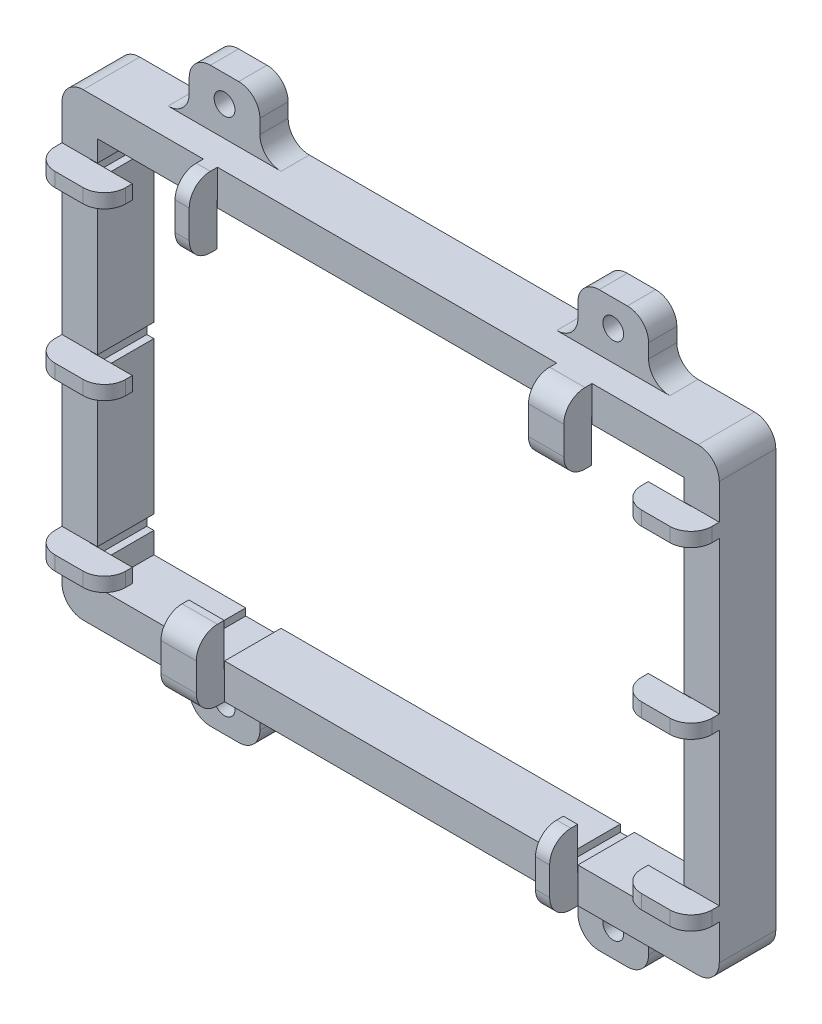
SolidWorks part; units mm, degrees
ref_plane "Front Plane" through (0, 0, 0) normal (0, 0, 1) x (1, 0, 0)
ref_plane "Top Plane" through (0, 0, 0) normal (0, 1, 0) x (1, 0, 0)
ref_plane "Right Plane" through (0, 0, 0) normal (1, 0, 0) x (0, 0, -1)
sketch "Sketch1" plane through (0, 0, 0) normal (0, 0, 1) x (1, 0, 0)
  line L0 (-41.5, 29.0054) -> (-46.5, 32.5) construction
  line L1 (41.5, -27.5) -> (-41.5, -27.5)
  line L2 (41.5, -27.5) -> (41.5, 27.5)
  line L3 (41.5, 27.5) -> (-41.5, 27.5)
  line L4 (-41.5, -27.5) -> (-41.5, 27.5)
  line L5 (0, -62.4654) -> (0, 68.7423) construction
  line L6 (-81.6773, -1.5) -> (70.6517, -1.5) construction
  line L7 (46.5, -32.5) -> (-46.5, -32.5)
  line L8 (46.5, -32.5) -> (46.5, 32.5)
  line L9 (46.5, 32.5) -> (-46.5, 32.5)
  line L10 (-46.5, -32.5) -> (-46.5, 32.5)
  line L11 (46.5, -32.5) -> (41.5, -29.0054) construction
  line L12 (46.5, 32.5) -> (41.5, 29.0054) construction
  line L13 (-41.5, -29.0054) -> (-46.5, -32.5) construction
  point P0 (0, 0)
  point P6 (0, 0)
  dimension "D1" = 83
  dimension "D2" = 55
  dimension "D3" = 5
  dimension "D4" = 5
  dimension "D5" = 5
  dimension "D6" = 5
extrude "Boss-Extrude1" add sketch "Sketch1" along normal blind 8
fillet "Fillet1" radius 3 4 edges at (-46.5, -32.5, 4) (-46.5, 32.5, 4) (46.5, -32.5, 4) (46.5, 32.5, 4)
sketch "Sketch2" plane through (0, 32.5, 0) normal (0, 1, 0) x (1, 0, 0)
  line L0 (-43.5, 0) -> (-43.5, -8) construction
  line L1 (-32.5, 0) -> (-22.5, 0)
  line L2 (-32.5, 0) -> (-32.5, -4)
  line L3 (-32.5, -4) -> (-22.5, -4)
  line L4 (-22.5, 0) -> (-22.5, -4)
  line L5 (-32.5, 0) -> (-22.5, -4) construction
  line L6 (-32.5, -4) -> (-22.5, 0) construction
  line L7 (22.5, 0) -> (32.5, 0)
  line L8 (22.5, 0) -> (22.5, -4)
  line L9 (22.5, -4) -> (32.5, -4)
  line L10 (32.5, 0) -> (32.5, -4)
  line L11 (22.5, 0) -> (32.5, -4) construction
  line L12 (22.5, -4) -> (32.5, 0) construction
  line L13 (43.5, -8) -> (43.5, 0) construction
  line L16 (43.5, 0) -> (-43.5, 0) construction
  line L17 (43.5, -8) -> (-43.5, -8) construction
  point P0 (-27.5, -2)
  point P5 (27.5, -2)
  dimension "D1" = 10
  dimension "D2" = 10
  dimension "D3" = 11
  dimension "D4" = 11
  dimension "D5" = 0
  dimension "D6" = 0
  dimension "D7" = 4
  dimension "D8" = 4
extrude "Boss-Extrude6" add sketch "Sketch2" along normal blind 8
mirror "Mirror2" about plane through (0, 0, 0) normal (0, 1, 0) of "Boss-Extrude6"
fillet "Fillet3" radius 3 8 edges at (32.5, -32.5, 2) (22.5, -32.5, 2) (-22.5, -32.5, 2) (-32.5, -32.5, 2) (-32.5, 32.5, 2) (-22.5, 32.5, 2) (22.5, 32.5, 2) (32.5, 32.5, 2)
sketch "Sketch9" plane through (0, 0, 4) normal (0, 0, 1) x (1, 0, 0)
  circle A1 centre (27.5, -36.7427) radius 1.47
  dimension "D1" = 2.94
extrude "Cut-Extrude1" cut sketch "Sketch9" against normal through all
mirror "Mirror3" about plane through (0, 0, 0) normal (1, 0, 0) of "Cut-Extrude1"
mirror "Mirror4" about plane through (0, 0, 0) normal (0, 1, 0) of "Mirror3", "Cut-Extrude1"
sketch "Sketch10" plane through (0, 0, 0) normal (0, 0, -1) x (-1, 0, 0)
  line L0 (41.5, -27.5) -> (-41.5, -27.5) construction
  line L1 (-24.5, -27.5) -> (-26.5, -27.5)
  line L2 (-24.5, -27.5) -> (-24.5, -28.5)
  line L3 (-24.5, -28.5) -> (-26.5, -28.5)
  line L4 (-26.5, -27.5) -> (-26.5, -28.5)
  line L5 (-41.5, -27.5) -> (-41.5, 27.5) construction
  line L7 (23.5, -27.5) -> (28.5, -27.5)
  line L8 (23.5, -27.5) -> (23.5, -28.5)
  line L9 (23.5, -28.5) -> (28.5, -28.5)
  line L10 (28.5, -27.5) -> (28.5, -28.5)
  line L13 (41.5, 27.5) -> (41.5, -27.5) construction
  dimension "D1" = 1
  dimension "D2" = 2
  dimension "D3" = 15
  dimension "D4" = 13
  dimension "D5" = 5
  dimension "D6" = 1
fillet "Fillet4" radius 3 8 edges at (-22.5, 40.5, 2) (-32.5, 40.5, 2) (22.5, 40.5, 2) (32.5, 40.5, 2) (32.5, -40.5, 2) (22.5, -40.5, 2) (-22.5, -40.5, 2) (-32.5, -40.5, 2)
extrude "Cut-Extrude2" cut sketch "Sketch10" against normal through all
sketch "Sketch11" plane through (0, 0, 0) normal (0, 0, -1) x (-1, 0, 0)
  line L0 (41.5, 27.5) -> (26.5, 27.5) construction
  line L1 (-41.5, 27.5) -> (41.5, 27.5) construction
  line L2 (-41.5, 27.5) -> (-28.5, 27.5) construction
  line L3 (26.5, 27.5) -> (24.5, 27.5)
  line L4 (26.5, 27.5) -> (26.5, 28.5)
  line L5 (26.5, 28.5) -> (24.5, 28.5)
  line L6 (24.5, 27.5) -> (24.5, 28.5)
  line L8 (-28.5, 27.5) -> (-23.5, 27.5)
  line L9 (-28.5, 27.5) -> (-28.5, 28.5)
  line L10 (-28.5, 28.5) -> (-23.5, 28.5)
  line L11 (-23.5, 27.5) -> (-23.5, 28.5)
  dimension "D1" = 15
  dimension "D2" = 2
  dimension "D3" = 1
  dimension "D4" = 13
  dimension "D5" = 1
  dimension "D6" = 5
extrude "Cut-Extrude3" cut sketch "Sketch11" against normal through all
sketch "Sketch12" plane through (0, 0, 0) normal (0, 0, -1) x (-1, 0, 0)
  line L0 (58.5237, 0) -> (-57.2606, 0) construction
  line L6 (-41.5, -27.5) -> (-41.5, 27.5) construction
  line L11 (-42.5, 1) -> (-41.5, 1)
  line L12 (-42.5, 1) -> (-42.5, -1)
  line L13 (-42.5, -1) -> (-41.5, -1)
  line L14 (-41.5, 1) -> (-41.5, -1)
  line L15 (-42.5, 1) -> (-41.5, -1) construction
  line L16 (-42.5, -1) -> (-41.5, 1) construction
  line L17 (-41.5, -27.5) -> (-41.5, -24.5) construction
  line L18 (-41.5, 27.5) -> (-41.5, 24.5) construction
  line L19 (-41.5, -24.5) -> (-42.5, -24.5)
  line L20 (-41.5, -24.5) -> (-41.5, -22.5)
  line L21 (-41.5, -22.5) -> (-42.5, -22.5)
  line L22 (-42.5, -24.5) -> (-42.5, -22.5)
  line L24 (-41.5, 24.5) -> (-42.5, 24.5)
  line L25 (-41.5, 24.5) -> (-41.5, 22.5)
  line L26 (-41.5, 22.5) -> (-42.5, 22.5)
  line L27 (-42.5, 24.5) -> (-42.5, 22.5)
  point P3 (-42, 0)
  dimension "D1" = 2
  dimension "D2" = 1
  dimension "D3" = 3
  dimension "D4" = 1
  dimension "D5" = 2
  dimension "D6" = 3
  dimension "D7" = 1
  dimension "D8" = 2
extrude "Cut-Extrude4" cut sketch "Sketch12" against normal through all
mirror "Mirror5" about plane through (0, 0, 0) normal (1, 0, 0) of "Cut-Extrude4"
sketch "Sketch14" plane through (0, 0, 8) normal (0, 0, 1) x (1, 0, 0)
  line L0 (46.5, -29.5) -> (46.5, 29.5) construction
  line L1 (42.5, 22.5) -> (46.5, 22.5)
  line L2 (42.5, 22.5) -> (42.5, 24.5)
  line L3 (42.5, 24.5) -> (46.5, 24.5)
  line L4 (46.5, 22.5) -> (46.5, 24.5)
  line L6 (42.5, -1) -> (46.5, -1)
  line L7 (42.5, -1) -> (42.5, 1)
  line L8 (42.5, 1) -> (46.5, 1)
  line L9 (46.5, -1) -> (46.5, 1)
  line L10 (42.5, -24.5) -> (46.5, -24.5)
  line L11 (42.5, -24.5) -> (42.5, -22.5)
  line L12 (42.5, -22.5) -> (46.5, -22.5)
  line L13 (46.5, -24.5) -> (46.5, -22.5)
  dimension "D1" = 2
  dimension "D2" = 2
  dimension "D3" = 2
extrude "Boss-Extrude14" add sketch "Sketch14" along normal blind 4
mirror "Mirror6" about plane through (0, 0, 0) normal (1, 0, 0) of "Boss-Extrude14"
sketch "Sketch15" plane through (42.5, 0, 0) normal (-1, 0, 0) x (0, 0, 1)
  line L0 (8, 24.5) -> (0, 24.5) construction
  line L5 (8.05, 24.5) -> (12, 24.5)
  line L6 (8.05, 24.5) -> (8.05, 22.5)
  line L7 (8.05, 22.5) -> (12, 22.5)
  line L8 (12, 24.5) -> (12, 22.5)
  line L14 (12, -1) -> (8, -1) construction
  line L15 (12, 1) -> (8.05, 1)
  line L16 (12, 1) -> (12, -1)
  line L17 (12, -1) -> (8.05, -1)
  line L18 (8.05, 1) -> (8.05, -1)
  line L19 (12, -24.5) -> (8, -24.5) construction
  line L20 (12, -22.5) -> (8.05, -22.5)
  line L21 (12, -22.5) -> (12, -24.5)
  line L22 (12, -24.5) -> (8.05, -24.5)
  line L23 (8.05, -22.5) -> (8.05, -24.5)
  dimension "D1" = 3.95
  dimension "D2" = 3.95
  dimension "D3" = 3.95
extrude "Boss-Extrude18" add sketch "Sketch15" along normal blind 6
mirror "Mirror7" about plane through (0, 0, 0) normal (1, 0, 0) of "Boss-Extrude18"
sketch "Sketch16" plane through (0, 0, 8) normal (0, 0, 1) x (1, 0, 0)
  line L0 (43.5, 32.5) -> (-43.5, 32.5) construction
  line L1 (-26.5, 28.5) -> (-24.5, 28.5)
  line L2 (-26.5, 28.5) -> (-26.5, 32.5)
  line L3 (-26.5, 32.5) -> (-24.5, 32.5)
  line L4 (-24.5, 28.5) -> (-24.5, 32.5)
  line L5 (-43.5, -32.5) -> (43.5, -32.5) construction
  line L6 (23.5, 28.5) -> (28.5, 28.5)
  line L7 (23.5, 28.5) -> (23.5, 32.5)
  line L8 (23.5, 32.5) -> (28.5, 32.5)
  line L9 (28.5, 28.5) -> (28.5, 32.5)
  line L10 (26.5, -28.5) -> (24.5, -28.5)
  line L11 (26.5, -28.5) -> (26.5, -32.5)
  line L12 (26.5, -32.5) -> (24.5, -32.5)
  line L13 (24.5, -28.5) -> (24.5, -32.5)
  line L15 (-28.5, -28.5) -> (-23.5, -28.5)
  line L16 (-28.5, -28.5) -> (-28.5, -32.5)
  line L17 (-28.5, -32.5) -> (-23.5, -32.5)
  line L18 (-23.5, -28.5) -> (-23.5, -32.5)
extrude "Boss-Extrude19" add sketch "Sketch16" along normal blind 4
sketch "Sketch17" plane through (0, 28.5, 0) normal (0, -1, 0) x (1, 0, 0)
  line L0 (-24.5, 12) -> (-24.5, 8) construction
  line L1 (-26.5, 12) -> (-24.5, 12)
  line L2 (-26.5, 12) -> (-26.5, 8.05)
  line L3 (-26.5, 8.05) -> (-24.5, 8.05)
  line L4 (-24.5, 12) -> (-24.5, 8.05)
  line L5 (28.5, 12) -> (28.5, 8) construction
  line L6 (23.5, 12) -> (28.5, 12)
  line L7 (23.5, 12) -> (23.5, 8.05)
  line L8 (23.5, 8.05) -> (28.5, 8.05)
  line L9 (28.5, 12) -> (28.5, 8.05)
  dimension "D1" = 3.95
  dimension "D2" = 3.95
extrude "Boss-Extrude20" add sketch "Sketch17" along normal blind 6
sketch "Sketch18" plane through (0, -28.5, 0) normal (0, 1, 0) x (1, 0, 0)
  line L0 (-28.5, -12) -> (-28.5, -8) construction
  line L1 (-23.5, -12) -> (-28.5, -12)
  line L2 (-23.5, -12) -> (-23.5, -8.05)
  line L3 (-23.5, -8.05) -> (-28.5, -8.05)
  line L4 (-28.5, -12) -> (-28.5, -8.05)
  line L5 (24.5, -12) -> (24.5, -8) construction
  line L6 (26.5, -12) -> (24.5, -12)
  line L7 (26.5, -12) -> (26.5, -8.05)
  line L8 (26.5, -8.05) -> (24.5, -8.05)
  line L9 (24.5, -12) -> (24.5, -8.05)
  dimension "D1" = 3.95
  dimension "D2" = 3.95
extrude "Boss-Extrude21" add sketch "Sketch18" along normal blind 6
fillet "Fillet6" radius 3 20 edges at (-25.5, 32.5, 12) (-25.5, 22.5, 12) (-36.5, 23.5, 12) (-46.5, 23.5, 12) (-36.5, 0, 12) (-46.5, 0, 12) (-36.5, -23.5, 12) (-46.5, -23.5, 12) (-26, -32.5, 12) (-26, -22.5, 12) (25.5, -32.5, 12) (25.5, -22.5, 12) (36.5, -23.5, 12) (46.5, -23.5, 12) (46.5, 0, 12) (36.5, 0, 12) (36.5, 23.5, 12) (26, 22.5, 12) (26, 32.5, 12) (46.5, 23.5, 12)
